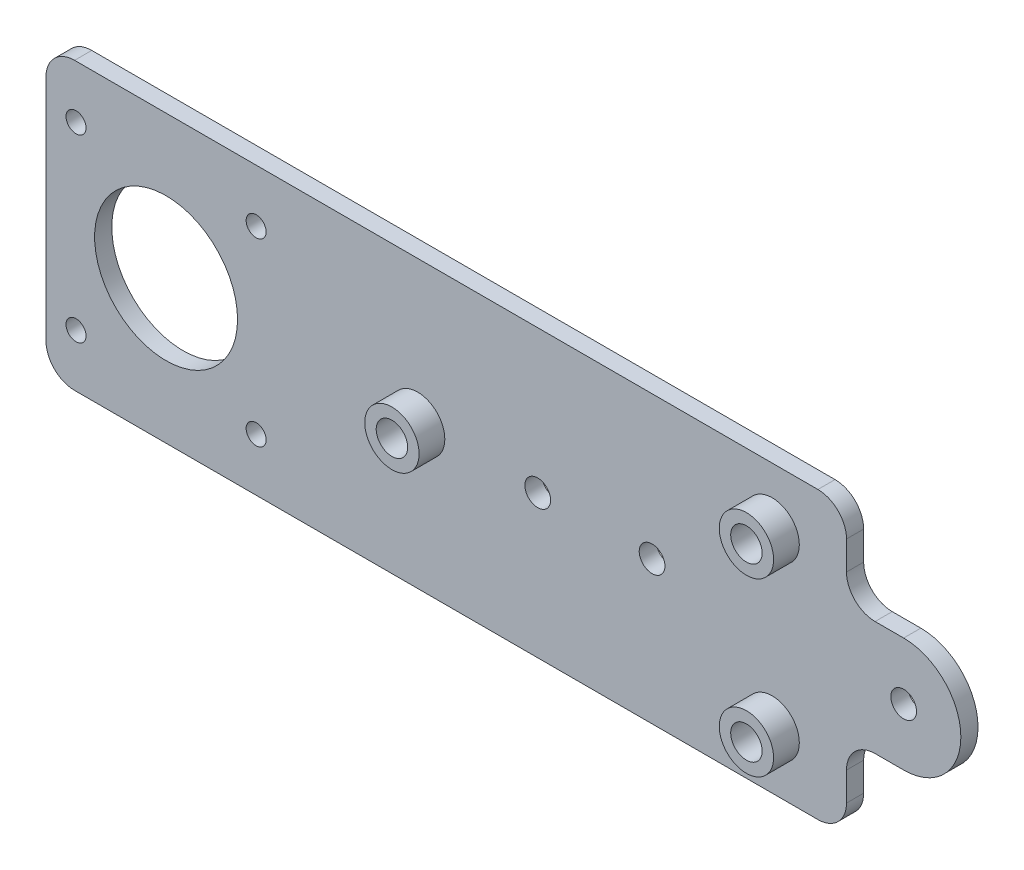
SolidWorks part; units mm, degrees
ref_plane "Front Plane" through (0, 0, 0) normal (0, 0, 1) x (1, 0, 0)
ref_plane "Top Plane" through (0, 0, 0) normal (0, 1, 0) x (1, 0, 0)
ref_plane "Right Plane" through (0, 0, 0) normal (1, 0, 0) x (0, 0, -1)
sketch "Sketch1" plane through (0, 0, 0) normal (0, 0, 1) x (1, 0, 0)
  line L1 (-65, 25) -> (65, 25)
  line L2 (-70, 20) -> (-70, -20)
  line L3 (-65, -25) -> (65, -25)
  line L4 (70, 20) -> (70, -20)
  line L5 (-70, 25) -> (70, -25) construction
  line L6 (-70, -25) -> (70, 25) construction
  arc A0 (65, -25) -> (70, -20) centre (65, -20) ccw
  arc A1 (65, 25) -> (70, 20) centre (65, 20) cw
  arc A2 (-70, -20) -> (-65, -25) centre (-65, -20) ccw
  arc A3 (-65, 25) -> (-70, 20) centre (-65, 20) ccw
  point P0 (0, 0)
  dimension "D3" = 5
  dimension "D1" = 50
  dimension "D2" = 140
extrude "Boss-Extrude1" add sketch "Sketch1" along normal blind 3
sketch "Sketch2" plane through (0, 0, 3) normal (0, 0, 1) x (1, 0, 0)
  line L0 (-49, 0) -> (0, 0) construction
  line L1 (-33.25, 15.75) -> (-64.75, 15.75) construction
  line L2 (-33.25, 15.75) -> (-33.25, -15.75) construction
  line L3 (-33.25, -15.75) -> (-64.75, -15.75) construction
  line L4 (-64.75, 15.75) -> (-64.75, -15.75) construction
  line L5 (-33.25, 15.75) -> (-64.75, -15.75) construction
  line L6 (-33.25, -15.75) -> (-64.75, 15.75) construction
  line L7 (-70, 20) -> (-70, -20) construction
  line L8 (57, 15) -> (57, -15) construction
  line L9 (0, 0) -> (57, 0) construction
  line L10 (70, -20) -> (70, 20) construction
  circle A0 centre (-64.75, 15.75) radius 1.75
  circle A1 centre (-33.25, 15.75) radius 1.75
  circle A2 centre (-64.75, -15.75) radius 1.75
  circle A3 centre (-33.25, -15.75) radius 1.75
  circle A4 centre (-49, 0) radius 12.5
  circle A5 centre (57, 15) radius 2.75
  circle A6 centre (57, -15) radius 2.75
  circle A7 centre (-5, 0) radius 2.75
  point P0 (-49, 0)
  dimension "D1" = 3.5
  dimension "D4" = 25
  dimension "D5" = 5.5
  dimension "D2" = 31.5
  dimension "D3" = 21
  dimension "D6" = 30
  dimension "D7" = 13
  dimension "D8" = 62
extrude "Cut-Extrude1" cut sketch "Sketch2" against normal blind 3
sketch "Sketch3" plane through (0, 0, 3) normal (0, 0, 1) x (1, 0, 0)
  circle A3 centre (57, 15) radius 2.75 construction
  circle A4 centre (57, 15) radius 2.75
  circle A5 centre (57, 15) radius 4.75
  circle A6 centre (-5, 0) radius 2.75 construction
  circle A7 centre (57, -15) radius 2.75 construction
  circle A8 centre (-5, 0) radius 2.75
  circle A9 centre (57, -15) radius 2.75
  circle A10 centre (-5, 0) radius 4.75
  circle A11 centre (57, -15) radius 4.75
  dimension "D1" = 2
  dimension "D2" = 2
extrude "Boss-Extrude2" add sketch "Sketch3" along normal blind 4.5
sketch "Sketch4" plane through (0, 0, 0) normal (0, 0, 1) x (1, 0, 0)
  line L0 (70, 10) -> (70, -10)
  line L1 (70, -20) -> (70, 20) construction
  line L2 (0, 0) -> (70, 0) construction
  line L3 (70, 10) -> (80, 10)
  line L4 (70, -10) -> (80, -10)
  line L5 (80, 10) -> (80, -10) construction
  arc A0 (80, -10) -> (80, 10) centre (80, 0) ccw
  circle A1 centre (80, 0) radius 2.25
  dimension "D3" = 4.5
  dimension "D1" = 20
  dimension "D2" = 10
extrude "Boss-Extrude3" add sketch "Sketch4" along normal blind 3 contours L4 A0 L3 L0
fillet "Fillet1" radius 5 2 edges at (70, -10, 1.5) (70, 10, 1.5)
sketch "Sketch5" plane through (0, 0, 3) normal (0, 0, 1) x (1, 0, 0)
  line L0 (-5, 0) -> (57, 0) construction
  line L1 (57, 0) -> (57, -15) construction
  circle A0 centre (16, 0) radius 2.25
  circle A1 centre (36, 0) radius 2.25
  point P10 (26, 0)
  dimension "D3" = 4.5
  dimension "D1" = 10
  dimension "D2" = 10
extrude "Cut-Extrude2" cut sketch "Sketch5" against normal through all
